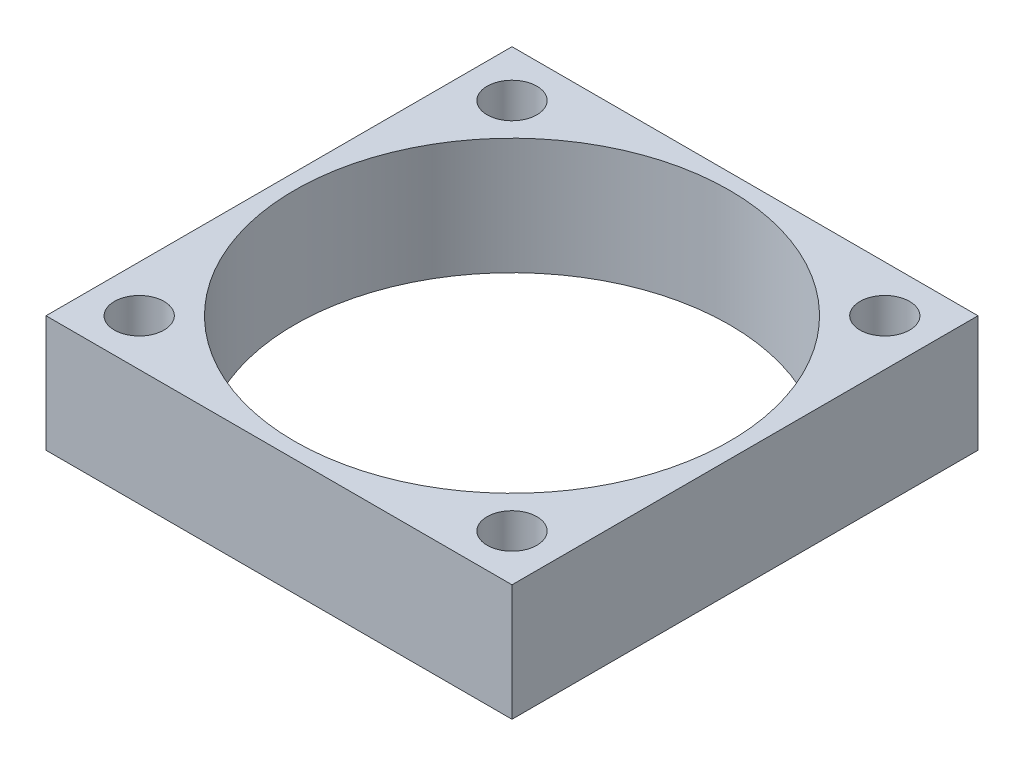
SolidWorks part; units mm, degrees
ref_plane "Front Plane" through (0, 0, 0) normal (0, 0, 1) x (1, 0, 0)
ref_plane "Top Plane" through (0, 0, 0) normal (0, 1, 0) x (1, 0, 0)
ref_plane "Right Plane" through (0, 0, 0) normal (1, 0, 0) x (0, 0, -1)
sketch "Sketch1" plane through (0, 0, 0) normal (0, 1, 0) x (1, 0, 0)
  line L0 (15, 30) -> (15, 0) construction
  line L1 (0, 0) -> (30, 0)
  line L2 (0, 0) -> (0, 30)
  line L3 (0, 30) -> (30, 30)
  line L4 (30, 0) -> (30, 30)
  line L5 (0, 15) -> (30, 15) construction
  circle A0 centre (3, 27) radius 1.6
  circle A1 centre (27, 27) radius 1.6
  circle A2 centre (27, 3) radius 1.6
  circle A3 centre (3, 3) radius 1.6
  circle A4 centre (15, 15) radius 14
  dimension "D3" = 3.2
  dimension "D6" = 28
  dimension "D1" = 30
  dimension "D2" = 30
  dimension "D4" = 24
  dimension "D5" = 24
extrude "Boss-Extrude1" add sketch "Sketch1" along normal blind 7.5
